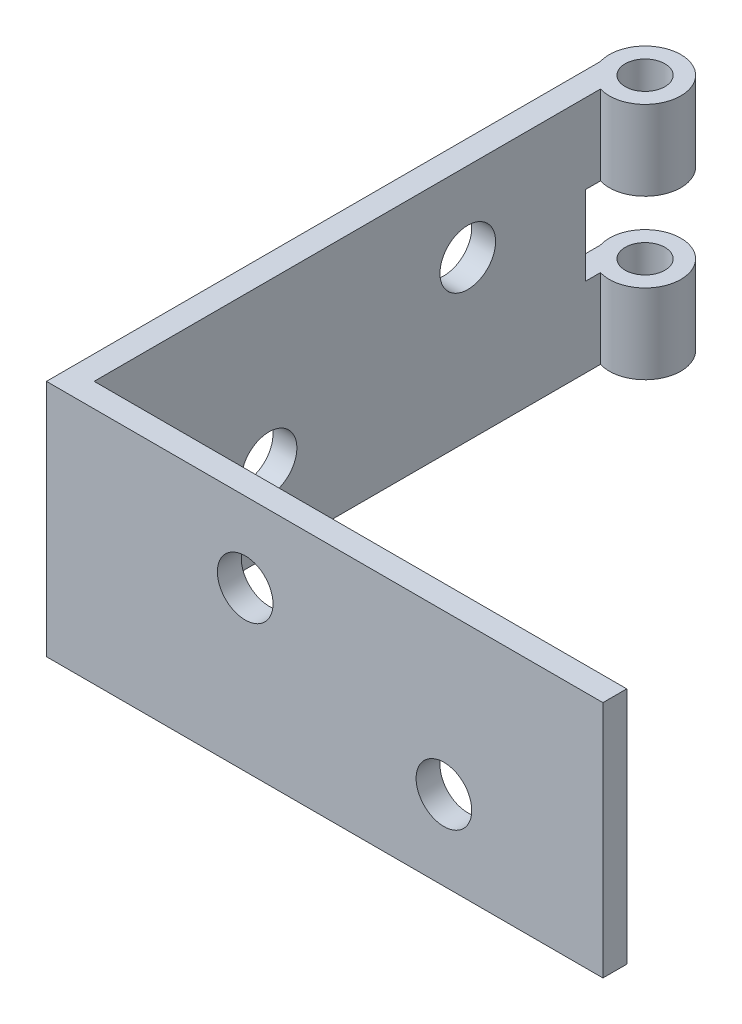
SolidWorks part; units mm, degrees
ref_plane "Спереди" through (0, 0, 0) normal (0, 0, 1) x (1, 0, 0)
ref_plane "Сверху" through (0, 0, 0) normal (0, 1, 0) x (1, 0, 0)
ref_plane "Справа" through (0, 0, 0) normal (1, 0, 0) x (0, 0, -1)
sketch "Эскиз1" plane through (0, 0, 0) normal (0, 1, 0) x (1, 0, 0)
  line L0 (0, 0) -> (70, 0)
  line L1 (0, 0) -> (0, 70)
extrude "Вытянуть-Тонкостенный1" add sketch "Эскиз1" along normal blind 30 thin thin type one direction wall 3
sketch "Эскиз2" plane through (0, 0, 0) normal (-1, 0, 0) x (0, 0, 1)
  circle A1 centre (-50, 20) radius 3.5
  circle A2 centre (-25, 10) radius 3.5
extrude "Вырез-Вытянуть1" cut sketch "Эскиз2" against normal through all
sketch "Эскиз3" plane through (0, 0, 0) normal (0, 0, 1) x (1, 0, 0)
  circle A0 centre (25, 20) radius 3.5
  circle A1 centre (50, 10) radius 3.5
extrude "Вырез-Вытянуть2" cut sketch "Эскиз3" against normal through all
sketch "Эскиз4" plane through (0, 0, 0) normal (0, 1, 0) x (1, 0, 0)
  circle A0 centre (4.3, 71) radius 4.5
  point P3 (0, 0)
extrude "Вытянуть-Тонкостенный2" add sketch "Эскиз4" along normal blind 30 thin thin type one direction reverse wall 2
sketch "Эскиз5" plane through (0, 0, 0) normal (0, 1, 0) x (1, 0, 0)
  circle A0 centre (4.3, 71) radius 2.5
extrude "Вырез-Вытянуть6" cut sketch "Эскиз5" along normal through all
sketch "Эскиз6" plane through (0, 0, 0) normal (1, 0, 0) x (0, 0, -1)
  line L1 (64.8246, 19.9893) -> (76.8023, 19.9893)
  line L2 (64.8246, 19.9893) -> (64.8246, 10)
  line L3 (64.8246, 10) -> (76.8023, 10)
  line L4 (76.8023, 19.9893) -> (76.8023, 10)
  point P4 (66.5, 20.149)
  point P5 (0, 0)
  point P6 (0, 0)
  point P7 (0, 0)
  point P8 (0, 0)
  point P9 (0, 0)
  point P10 (66.5, 20.1722)
  point P11 (64.8246, 19.9893)
extrude "Вырез-Вытянуть8" cut sketch "Эскиз6" against normal through all both and the other way through all
